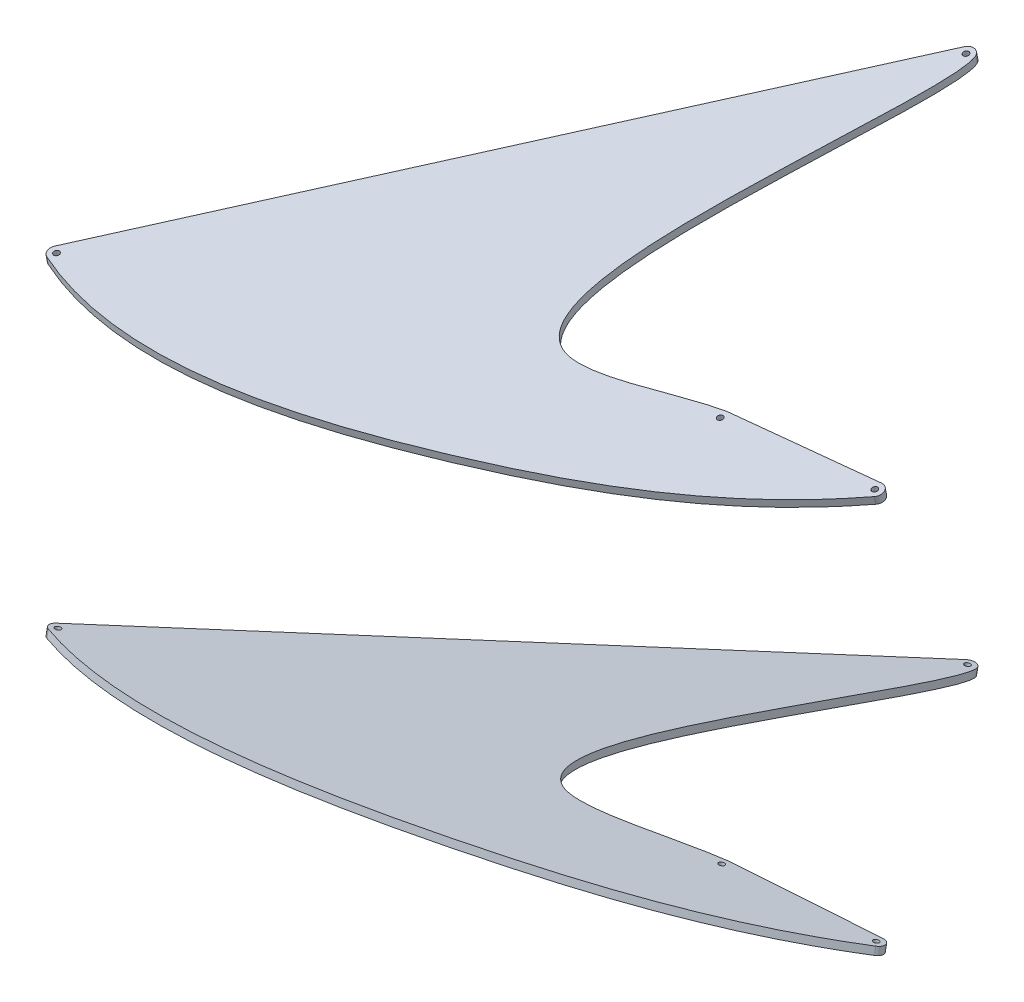
SolidWorks part; units mm, degrees
material "Elastyczna pianka poliuretanowa"
ref_plane "Płaszczyzna XY" through (0, 0, 0) normal (0, 0, 1) x (1, 0, 0)
ref_plane "Płaszczyzna XZ" through (0, 0, 0) normal (0, 1, 0) x (1, 0, 0)
ref_plane "Płaszczyzna YZ" through (0, 0, 0) normal (1, 0, 0) x (0, 0, -1)
ref_plane "Płaszczyzna1" through (0, -365.9457, 71.1326) normal (0, 0.9816, -0.1908) x (1, 0, 0)
sketch "Szkic1" plane through (0, -365.9457, 71.1326) normal (0, 0.9816, -0.1908) x (1, 0, 0)
  line L1 (1634.8716, -794.9597) -> (1483.1737, -808.8534)
  line L2 (939.3713, -984.0725) -> (1348.4905, -414.167)
  circle A11 centre (1483.9034, -816.82) radius 3
  circle A14 centre (1634.8716, -802.9597) radius 3
  arc A20 (1640.2813, -808.8534) -> (1633.4184, -795.0928) centre (1634.8716, -802.9597) ccw
  circle A21 centre (945.8701, -988.7378) radius 3
  arc A22 (939.3713, -984.0725) -> (942.8113, -996.1299) centre (945.8701, -988.7378) ccw
  arc A23 (1362.2836, -415.547) -> (1348.4905, -414.167) centre (1354.9893, -418.8323) ccw
  circle A24 centre (1354.9893, -418.8323) radius 3
  spline S0 degree 3 poles (942.8113, -996.1299) (1065.4306, -1046.8696) (1335.8064, -985.7121) (1556.4999, -885.756) (1640.2813, -808.8534) knots 0 0 0 0 0.548325 1 1 1 1
  spline S1 degree 3 poles (1483.1737, -808.8534) (1437.4698, -816.5628) (1275.8792, -890.62) (1317.9137, -619.9831) (1370.5074, -433.8062) (1362.2836, -415.547) knots 0 0 0 0 0.258279 0.641643 1 1 1 1
  dimension "D1" = 16
  dimension "D4" = 6
  dimension "D6" = 6
  dimension "D7" = 6
  dimension "D8" = 16
  dimension "D9" = 16
  dimension "D10" = 6
extrude "Dodanie-wyciągnięcie1" add sketch "Szkic1" along normal blind 8
mirror "Lustro2" about plane through (0, 0, 0) normal (0, 1, 0) of bodies 102
